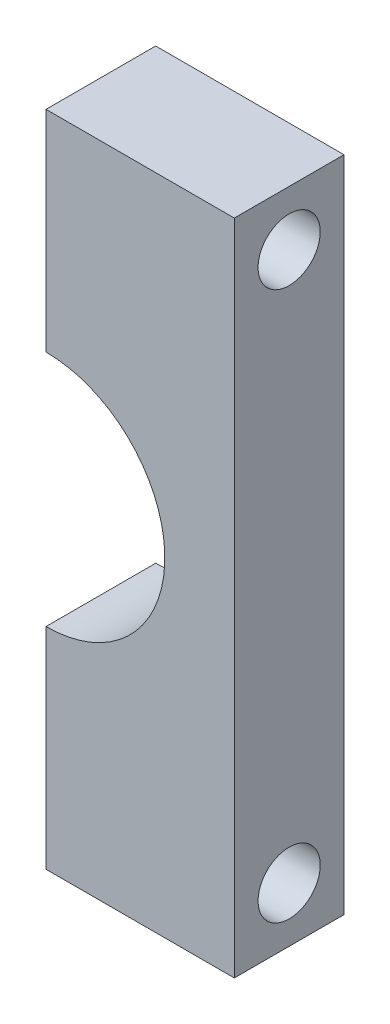
SolidWorks part; units mm, degrees
ref_plane "Front Plane" through (0, 0, 0) normal (0, 0, 1) x (1, 0, 0)
ref_plane "Top Plane" through (0, 0, 0) normal (0, 1, 0) x (1, 0, 0)
ref_plane "Right Plane" through (0, 0, 0) normal (1, 0, 0) x (0, 0, -1)
sketch "Sketch1" plane through (0, 0, 0) normal (0, 0, 1) x (1, 0, 0)
  line L0 (0, 122.5) -> (0, 180)
  line L1 (0, 0) -> (51.5, 0)
  line L2 (0, 0) -> (0, 57.5)
  line L3 (0, 180) -> (51.5, 180)
  line L4 (51.5, 0) -> (51.5, 180)
  arc A0 (0, 57.5) -> (0, 122.5) centre (0, 90) ccw
  dimension "D3" = 32.5
  dimension "D4" = 90
  dimension "D1" = 180
  dimension "D2" = 51.5
extrude "Boss-Extrude1" add sketch "Sketch1" along normal blind 30
sketch "Sketch2" plane through (0, 0, 0) normal (-1, 0, 0) x (0, 0, 1)
  line L0 (30, 0) -> (0, 0) construction
  line L1 (30, 57.5) -> (30, 0) construction
  circle A0 centre (15, 15) radius 8.5
  dimension "D1" = 17
  dimension "D2" = 15
  dimension "D3" = 15
extrude "Cut-Extrude1" cut sketch "Sketch2" against normal through all
pattern_linear "LPattern1" count 2 spacing 150 along (0, 1, 0) of "Cut-Extrude1"
sketch "Sketch3" plane through (0, 0, 0) normal (-1, 0, 0) x (0, 0, 1)
  line L0 (0, 57.5) -> (0, 0) construction
  circle A0 centre (15, 48.5) radius 4.75
  circle A1 centre (15, 15) radius 8.5 construction
  dimension "D1" = 9.5
  dimension "D2" = 33.5
  dimension "D3" = 15
extrude "Cut-Extrude2" cut sketch "Sketch3" against normal blind 15
pattern_linear "LPattern2" count 2 spacing 83 along (0, 1, 0) of "Cut-Extrude2"
